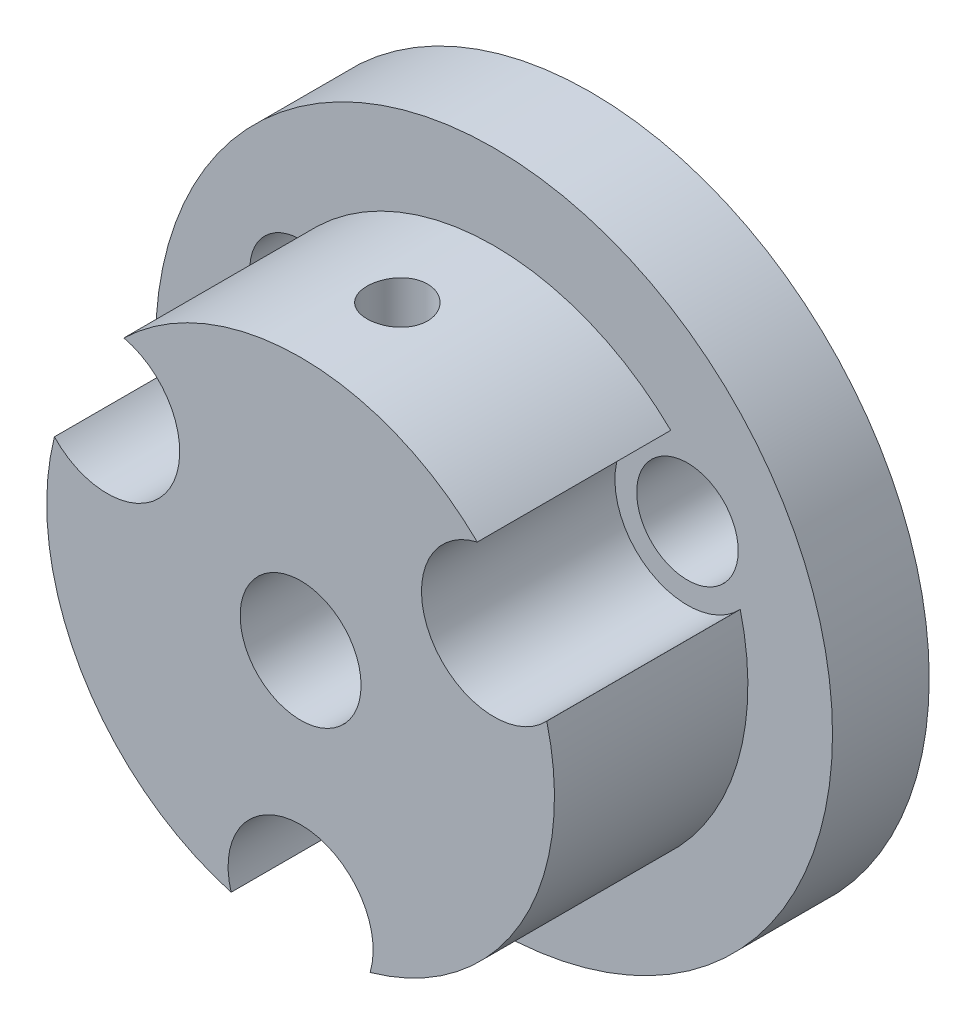
SolidWorks part; units mm, degrees
ref_plane "Ebene vorne" through (0, 0, 0) normal (0, 0, 1) x (1, 0, 0)
ref_plane "Ebene oben" through (0, 0, 0) normal (0, 1, 0) x (1, 0, 0)
ref_plane "Ebene rechts" through (0, 0, 0) normal (1, 0, 0) x (0, 0, -1)
sketch "Skizze1" plane through (0, 0, 0) normal (0, 0, 1) x (1, 0, 0)
  circle A0 centre (0, 0) radius 14
  dimension "D1" = 28
extrude "Aufsatz-Linear austragen1" add sketch "Skizze1" along normal blind 4
sketch "Skizze3" plane through (0, 0, 4) normal (0, 0, 1) x (1, 0, 0)
  line L1 (8, 4.6188) -> (-8, 4.6188) construction
  line L2 (-8, 4.6188) -> (0, -9.2376) construction
  line L3 (0, -9.2376) -> (8, 4.6188) construction
  circle A0 centre (0, 0) radius 9.2376 construction
  circle A1 centre (-8, 4.6188) radius 2.1
  circle A2 centre (8, 4.6188) radius 2.1
  circle A3 centre (0, -9.2376) radius 2.1
  dimension "D1" = 16
  dimension "D2" = 4.2
extrude "Schnitt-Linear austragen1" cut sketch "Skizze3" against normal through all
sketch "Skizze2" plane through (0, 0, 4) normal (0, 0, 1) x (1, 0, 0)
  circle A0 centre (0, 0) radius 10.5
  dimension "D1" = 21
extrude "Aufsatz-Linear austragen2" add sketch "Skizze2" along normal blind 8
sketch "Skizze5" plane through (0, 0, 4) normal (0, 0, -1) x (-1, 0, 0)
  circle A0 centre (-8, 4.6188) radius 3
  circle A1 centre (8, 4.6188) radius 3
  circle A2 centre (0, -9.2376) radius 3
  dimension "D1" = 6
extrude "Schnitt-Linear austragen2" cut sketch "Skizze5" against normal up to next
sketch "Skizze6" plane through (0, 0, 12) normal (0, 0, 1) x (1, 0, 0)
  circle A0 centre (0, 0) radius 2.5
  dimension "D1" = 5
extrude "Schnitt-Linear austragen3" cut sketch "Skizze6" against normal through all
ref_plane "Ebene1" through (0, 10.5, 0) normal (0, 1, 0) x (1, 0, 0)
sketch "Skizze7" plane through (0, 10.5, 0) normal (0, 1, 0) x (1, 0, 0)
  line L0 (0, -4) -> (0, -12) construction
  line L1 (-7.3093, -4) -> (7.3093, -4) construction
  line L2 (-7.3093, -12) -> (7.3093, -12) construction
  circle A0 centre (0, -8) radius 1.25
  dimension "D1" = 2.5
extrude "Schnitt-Linear austragen4" cut sketch "Skizze7" against normal up to next
